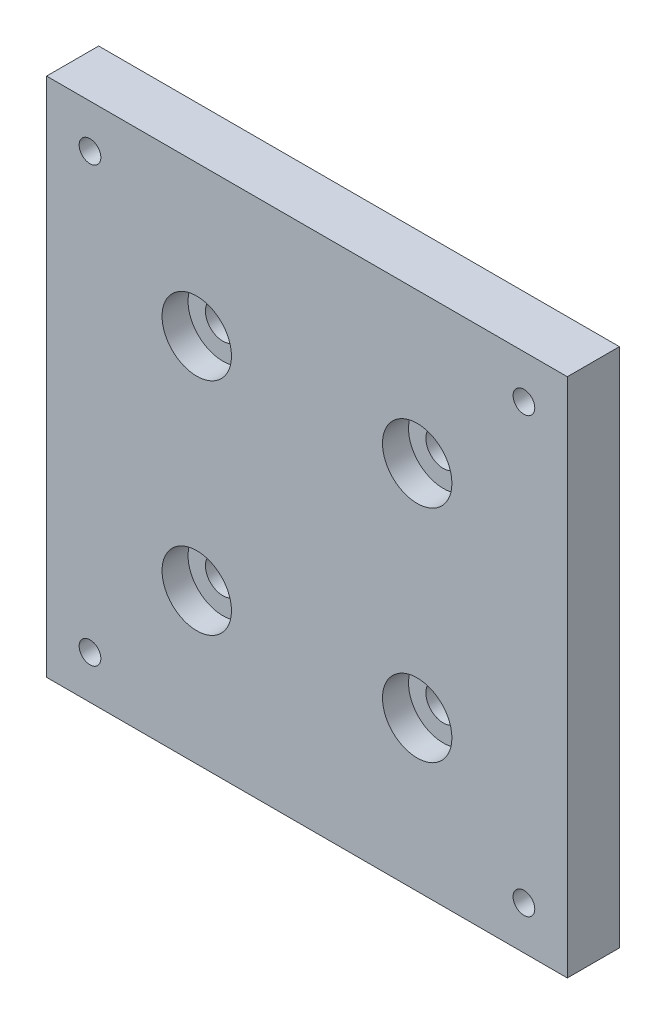
SolidWorks part; units mm, degrees
ref_plane "前视基准面" through (0, 0, 0) normal (0, 0, 1) x (1, 0, 0)
ref_plane "上视基准面" through (0, 0, 0) normal (0, 1, 0) x (1, 0, 0)
ref_plane "右视基准面" through (0, 0, 0) normal (1, 0, 0) x (0, 0, -1)
sketch "草图1" plane through (0, 0, 0) normal (0, 0, 1) x (1, 0, 0)
  line L1 (-30, 30) -> (30, 30)
  line L2 (-30, 30) -> (-30, -30)
  line L3 (-30, -30) -> (30, -30)
  line L4 (30, 30) -> (30, -30)
  line L5 (-30, 30) -> (30, -30) construction
  line L6 (-30, -30) -> (30, 30) construction
  point P0 (0, 0)
  dimension "D1" = 60
extrude "凸台-拉伸1" add sketch "草图1" along normal blind 6
sketch "草图2" plane through (0, 0, 6) normal (0, 0, 1) x (1, 0, 0)
  line L1 (25, -25) -> (-25, -25) construction
  line L2 (25, -25) -> (25, 25) construction
  line L3 (25, 25) -> (-25, 25) construction
  line L4 (-25, -25) -> (-25, 25) construction
  line L5 (25, -25) -> (-25, 25) construction
  line L6 (25, 25) -> (-25, -25) construction
  line L7 (12.7, -12.7) -> (-12.7, -12.7) construction
  line L8 (12.7, -12.7) -> (12.7, 12.7) construction
  line L9 (12.7, 12.7) -> (-12.7, 12.7) construction
  line L10 (-12.7, -12.7) -> (-12.7, 12.7) construction
  line L11 (12.7, -12.7) -> (-12.7, 12.7) construction
  line L12 (12.7, 12.7) -> (-12.7, -12.7) construction
  point P0 (0, 0)
  point P6 (0, 0)
  dimension "D1" = 25.4
  dimension "D2" = 50
hole_wizard "M3 螺纹孔1" positions "3D草图1" profile "草图3" tap size "M3" standard "ISO" end condition through all
sketch3d "3D草图1"
  point P0 (-25, 25, 6)
  point P3 (25, 25, 6)
  point P6 (25, -25, 6)
  point P9 (-25, -25, 6)
sketch "草图3" plane through (-25, 25, 6) normal (1, 0, 0) x (0, -1, 0)
  line L0 (0, 0) -> (0, 6)
  line L1 (0, 6) -> (1.25, 6)
  line L2 (1.25, 6) -> (1.25, 0)
  line L5 (1.25, 0) -> (0, 0)
  line L11 (0, -6.35) -> (0, 107.95) construction
  dimension "通孔螺纹孔钻头直径" = 2.5
  dimension "通孔螺纹孔钻头深度" = 6
cosmetic thread "孔螺蚊线1"
cosmetic thread "孔螺蚊线2"
cosmetic thread "孔螺蚊线3"
cosmetic thread "孔螺蚊线4"
hole_wizard "孔1" positions "3D草图2" profile "草图4" legacy end condition through all
sketch3d "3D草图2"
  point P0 (-12.7, 12.7, 6)
  point P3 (12.7, 12.7, 6)
  point P6 (12.7, -12.7, 6)
  point P9 (-12.7, -12.7, 6)
sketch "草图4" plane through (-12.7, 12.7, 6) normal (1, 0, 0) x (0, -1, 0)
  line L0 (0, 0) -> (0, 6)
  line L1 (0, 6) -> (2, 6)
  line L2 (2, 6) -> (2, 3)
  line L3 (2, 3) -> (4, 3)
  line L4 (4, 3) -> (4, 0)
  line L5 (4, 0) -> (0, 0)
  line L6 (0, 110) -> (0, -10) construction
  dimension "直径" = 4
  dimension "深度" = 6
  dimension "柱坑直径" = 8
  dimension "柱坑深度" = 3
